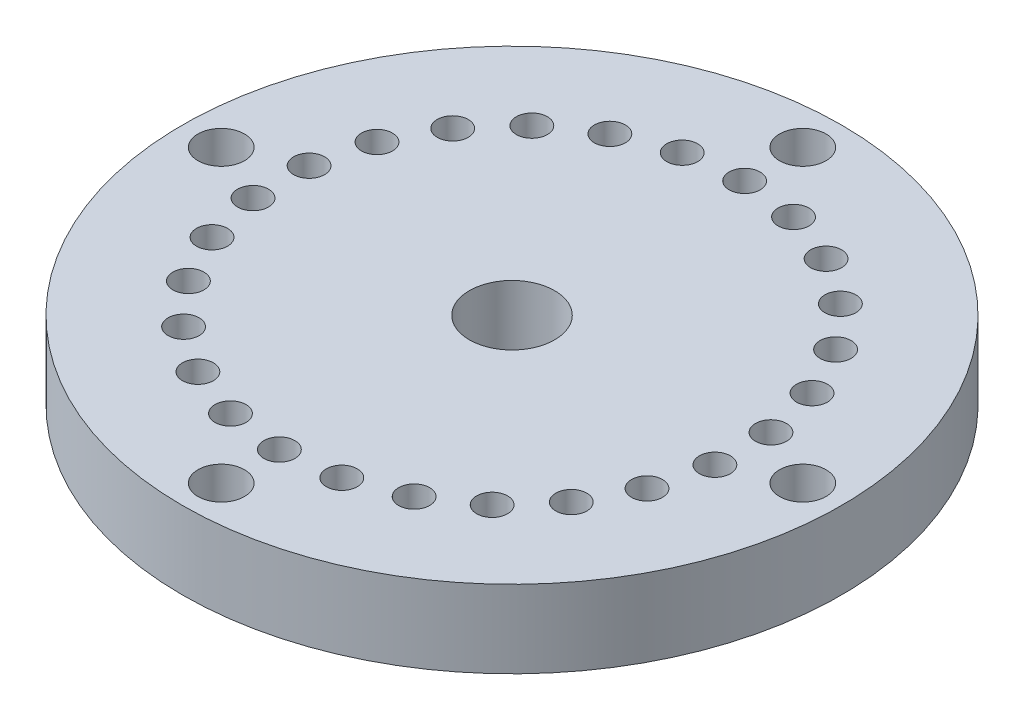
SolidWorks part; units mm, degrees
ref_plane "Plan de face" through (0, 0, 0) normal (0, 0, 1) x (1, 0, 0)
ref_plane "Plan de dessus" through (0, 0, 0) normal (0, 1, 0) x (1, 0, 0)
ref_plane "Plan de droite" through (0, 0, 0) normal (1, 0, 0) x (0, 0, -1)
sketch "Esquisse1" plane through (0, 0, 0) normal (0, 1, 0) x (1, 0, 0)
  circle A0 centre (0, 0) radius 4.25
  circle A1 centre (0, 0) radius 0.55
  circle A2 centre (0, 3) radius 0.2
  circle A3 centre (0, 3.75) radius 0.3
  circle A4 centre (0.7179, 2.9128) radius 0.2
  circle A5 centre (1.3942, 2.6564) radius 0.2
  circle A6 centre (1.9894, 2.2455) radius 0.2
  circle A7 centre (2.469, 1.7042) radius 0.2
  circle A8 centre (2.805, 1.0638) radius 0.2
  circle A9 centre (2.9781, 0.3616) radius 0.2
  circle A10 centre (2.9781, -0.3616) radius 0.2
  circle A11 centre (2.805, -1.0638) radius 0.2
  circle A12 centre (2.469, -1.7042) radius 0.2
  circle A13 centre (1.9894, -2.2455) radius 0.2
  circle A14 centre (1.3942, -2.6564) radius 0.2
  circle A15 centre (0.7179, -2.9128) radius 0.2
  circle A16 centre (0, -3) radius 0.2
  circle A17 centre (-0.7179, -2.9128) radius 0.2
  circle A18 centre (-1.3942, -2.6564) radius 0.2
  circle A19 centre (-1.9894, -2.2455) radius 0.2
  circle A20 centre (-2.469, -1.7042) radius 0.2
  circle A21 centre (-2.805, -1.0638) radius 0.2
  circle A22 centre (-2.9781, -0.3616) radius 0.2
  circle A23 centre (-2.9781, 0.3616) radius 0.2
  circle A24 centre (-2.805, 1.0638) radius 0.2
  circle A25 centre (-2.469, 1.7042) radius 0.2
  circle A26 centre (-1.9894, 2.2455) radius 0.2
  circle A27 centre (-1.3942, 2.6564) radius 0.2
  circle A28 centre (-0.7179, 2.9128) radius 0.2
  circle A29 centre (3.75, 0) radius 0.3
  circle A30 centre (0, -3.75) radius 0.3
  circle A31 centre (-3.75, 0) radius 0.3
  point P64 (0, 0)
  point P70 (0, 0)
  dimension "D1" = 8.5
  dimension "D2" = 1.1
  dimension "D3" = 3
  dimension "D4" = 3.75
  dimension "D5" = 26
  dimension "D7" = 0.6
  dimension "D6" = 4
extrude "Boss.-Extru.2" add sketch "Esquisse1" along normal blind 1
sketch "Esquisse2" plane through (0, 1, 0) normal (0, 1, 0) x (1, 0, 0)
sketch "Esquisse3" plane through (0, 1, 0) normal (0, 1, 0) x (1, 0, 0)
